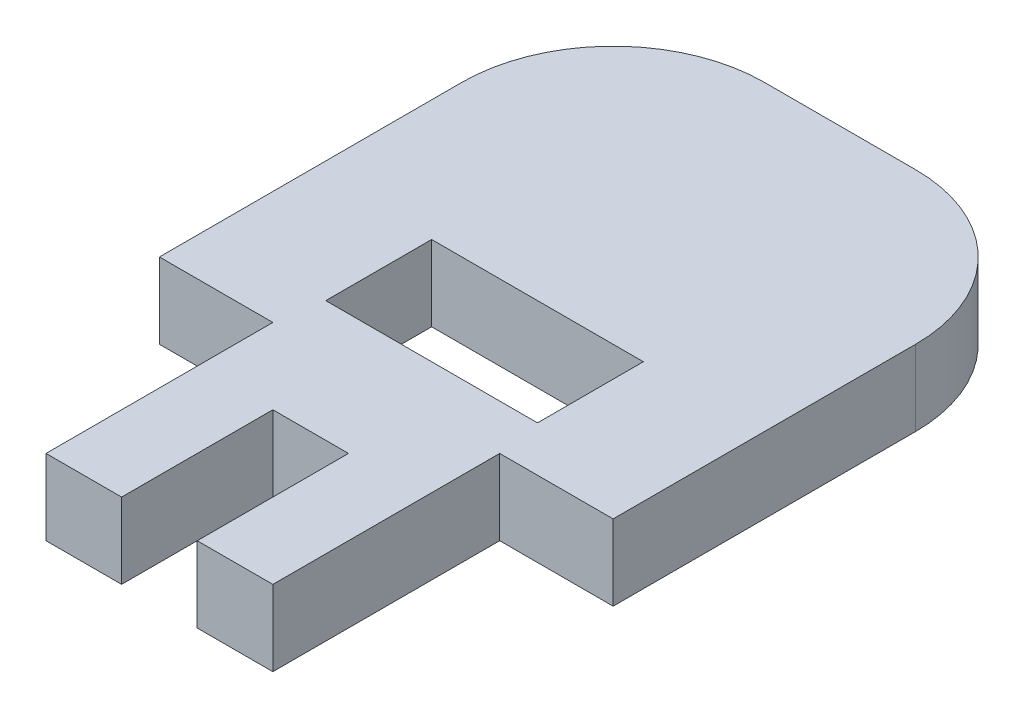
SolidWorks part; units mm, degrees
ref_plane "Front Plane" through (0, 0, 0) normal (0, 0, 1) x (1, 0, 0)
ref_plane "Top Plane" through (0, 0, 0) normal (0, 1, 0) x (1, 0, 0)
ref_plane "Right Plane" through (0, 0, 0) normal (1, 0, 0) x (0, 0, -1)
sketch "Sketch1" plane through (0, 0, 0) normal (0, 1, 0) x (1, 0, 0)
  line L0 (0, 41.275) -> (0, 3.175) construction
  line L1 (9.525, -3.175) -> (-9.525, -3.175)
  line L2 (9.525, -3.175) -> (9.525, 3.175)
  line L4 (-9.525, -3.175) -> (-9.525, 3.175)
  line L5 (9.525, -3.175) -> (-9.525, 3.175) construction
  line L6 (9.525, 3.175) -> (-9.525, -3.175) construction
  line L7 (-19.05, 3.175) -> (-9.525, 3.175)
  line L8 (-19.05, 3.175) -> (-19.05, 28.575)
  line L9 (-6.35, 41.275) -> (6.35, 41.275)
  line L10 (19.05, 3.175) -> (19.05, 28.575)
  line L11 (9.525, 3.175) -> (19.05, 3.175)
  arc A0 (6.35, 41.275) -> (19.05, 28.575) centre (6.35, 28.575) cw
  arc A1 (-19.05, 28.575) -> (-6.35, 41.275) centre (-6.35, 28.575) cw
  point P0 (0, 0)
  point P14 (19.05, 41.275)
  point P17 (-19.05, 41.275)
  dimension "D6" = 12.7
  dimension "D1" = 6.35
  dimension "D2" = 19.05
  dimension "D3" = 0
  dimension "D4" = 38.1
  dimension "D5" = 38.1
extrude "Boss-Extrude1" add sketch "Sketch1" along normal blind 6.35
sketch "Sketch2" plane through (0, 6.35, 0) normal (0, 1, 0) x (1, 0, 0)
  line L0 (-9.525, 3.175) -> (9.525, 3.175) construction
  line L1 (0, -3.175) -> (0, 3.175) construction
  line L2 (-9.525, -3.175) -> (9.525, -3.175) construction
  line L3 (0, 15.875) -> (0, 6.985) construction
  line L4 (-8.89, 15.875) -> (8.89, 15.875)
  line L5 (-8.89, 15.875) -> (-8.89, 6.985)
  line L6 (-8.89, 6.985) -> (8.89, 6.985)
  line L7 (8.89, 15.875) -> (8.89, 6.985)
  dimension "D1" = 0
  dimension "D2" = 17.78
  dimension "D3" = 8.89
  dimension "D4" = 3.81
extrude "Cut-Extrude1" cut sketch "Sketch2" against normal blind 6.35 contours L4 L7 L6 L5
sketch "Sketch3" plane through (0, 0, 3.175) normal (0, 0, 1) x (1, 0, 0)
  line L0 (-9.525, 0) -> (9.525, 0) construction
  line L1 (-9.525, 6.35) -> (-3.175, 6.35)
  line L2 (-9.525, 6.35) -> (-9.525, 0)
  line L3 (-9.525, 0) -> (-3.175, 0)
  line L4 (-3.175, 6.35) -> (-3.175, 0)
  line L5 (0, 6.35) -> (0, 0) construction
  line L6 (-9.525, 6.35) -> (9.525, 6.35) construction
  line L7 (9.525, 0) -> (3.175, 0)
  line L8 (3.175, 6.35) -> (3.175, 0)
  line L9 (9.525, 6.35) -> (3.175, 6.35)
  line L10 (9.525, 6.35) -> (9.525, 0)
  dimension "D1" = 6.35
extrude "Boss-Extrude2" add sketch "Sketch3" along normal blind 12.7
